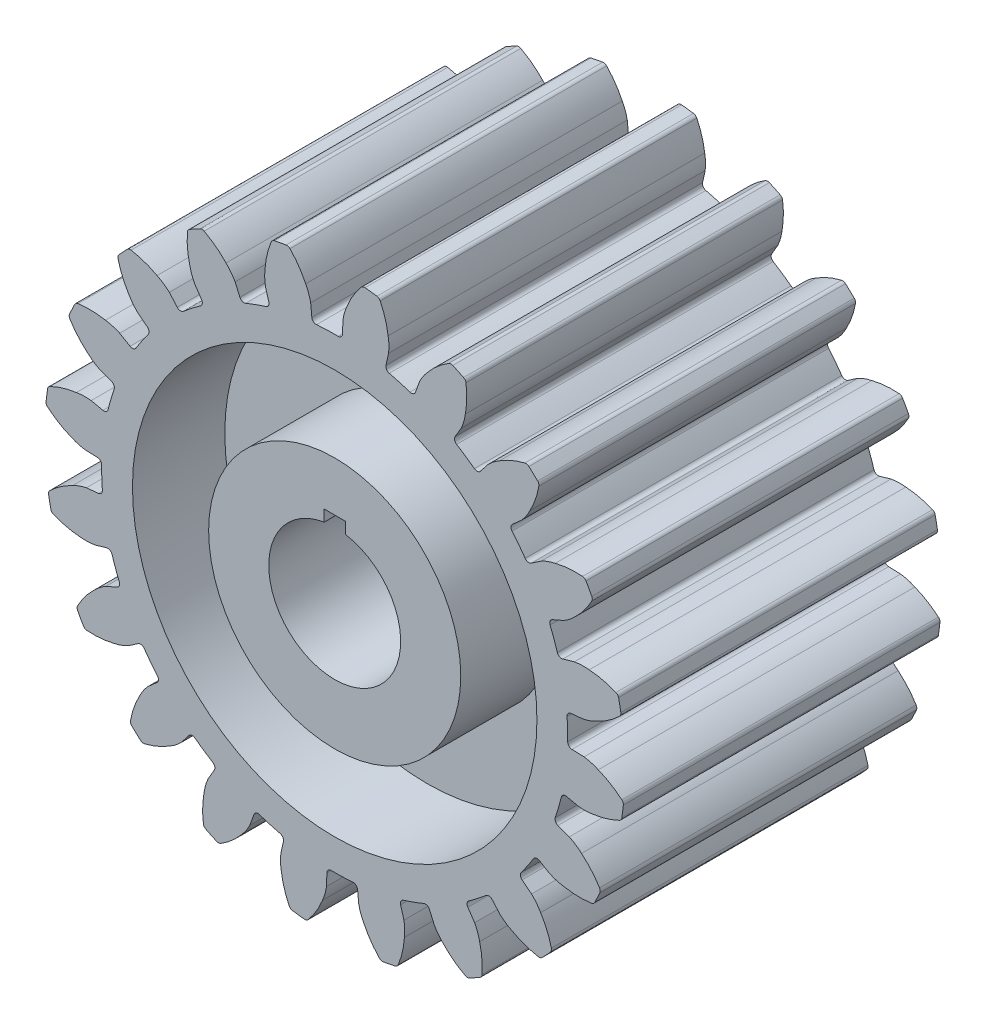
SolidWorks part; units mm, degrees
material "Ferro dúctil"
ref_plane "Plano frontal" through (0, 0, 0) normal (0, 0, 1) x (1, 0, 0)
ref_plane "Plano superior" through (0, 0, 0) normal (0, 1, 0) x (1, 0, 0)
ref_plane "Plano direito" through (0, 0, 0) normal (1, 0, 0) x (0, 0, -1)
sketch "Esboço1" plane through (0, 0, 0) normal (0, 0, 1) x (1, 0, 0)
  line L0 (30.783, 89.4002) -> (30.7831, 89.4005)
  line L3 (0, 88.33) -> (0, 0) construction
  line L5 (42.4148, 90.2189) -> (42.5459, 90.4978) construction
  line L6 (32.1638, 88.9127) -> (30.6102, 84.6181)
  line L7 (47.9488, 81.4917) -> (45.6328, 77.5555)
  arc A2 (47.9488, 81.4917) -> (49.5143, 86.8811) centre (30.783, 89.4002) ccw
  arc A4 (48.8393, 98.5633) -> (44.7419, 100.4896) centre (0, 0) ccw
  arc A5 (49.5143, 86.8811) -> (49.7513, 97.3014) centre (18.0682, 92.8091) ccw
  arc A6 (32.1638, 88.9127) -> (35.3152, 93.5566) centre (49.2051, 80.7394) cw
  arc A7 (35.3152, 93.5566) -> (43.1883, 100.3869) centre (59.9418, 73.123) cw
  arc A9 (28.501, 83.6055) -> (46.1987, 75.2853) centre (0, 0) ccw
  arc A10 (46.1987, 75.2853) -> (45.6328, 77.5555) centre (47.0721, 76.7086) cw
  arc A11 (28.501, 83.6055) -> (30.6102, 84.6181) centre (29.0398, 85.1862) ccw
  arc A12 (43.1883, 100.3869) -> (44.7419, 100.4896) centre (44.0626, 98.964) cw
  arc A13 (49.7513, 97.3014) -> (48.8393, 98.5633) centre (48.0978, 97.0669) ccw
  point P7 (0, 100)
  point P10 (0, 100)
  point P12 (30.783, 89.4002)
  point P16 (43.948, 100.8394)
  point P28 (49.6151, 98.1751)
  dimension "D1" = 1.67
  dimension "D2" = 1.67
  dimension "D5" = 176.66
extrude "Ressalto-extrusão1" add sketch "Esboço1" along normal mid plane 120 contours A9 A10 L7 A2 A5 A13 A4 A12 A7 A6 L6 A11
pattern_circular "PadrãoCircular1" count 20 over 360 about axis through (0, 0, 0) along (0, 0, 1) of "Ressalto-extrusão1"
sketch "Esboço2" plane through (0, 0, 60) normal (0, 0, 1) x (1, 0, 0)
  line L2 (4, 24.6779) -> (4, 29)
  line L3 (4, 29) -> (-4, 29)
  line L4 (-4, 24.6779) -> (-4, 29)
  arc A0 (-4, 24.6779) -> (4, 24.6779) centre (0, 0) ccw
  point P3 (0, 9.7411)
  dimension "D1" = 8
  dimension "D3" = 29
extrude "Corte-extrusão1" cut sketch "Esboço2" against normal blind 120
sketch "Esboço3" plane through (0, 0, 60) normal (0, 0, 1) x (1, 0, 0)
  circle A0 centre (0, 0) radius 47.7796
  circle A1 centre (0, 0) radius 76.6527
extrude "Corte-extrusão2" cut sketch "Esboço3" against normal blind 35
sketch "Esboço4" plane through (0, 0, -60) normal (0, 0, -1) x (-1, 0, 0)
  circle A0 centre (0, 0) radius 47.7796 construction
  circle A1 centre (0, 0) radius 76.6527 construction
  circle A2 centre (0, 0) radius 47.7796
  circle A3 centre (0, 0) radius 76.6527
extrude "Corte-extrusão3" cut sketch "Esboço4" against normal blind 35
